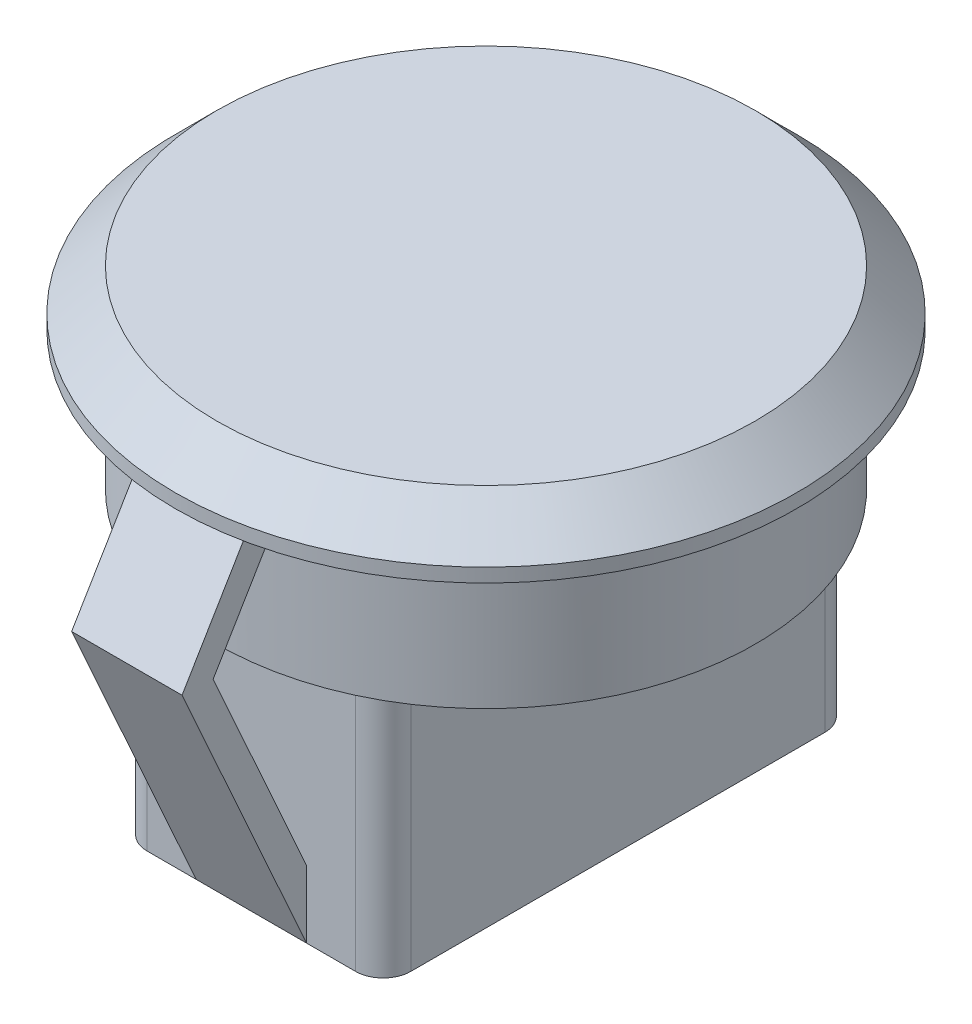
SolidWorks part; units mm, degrees
ref_plane "Спереди" through (0, 0, 0) normal (0, 0, 1) x (1, 0, 0)
ref_plane "Сверху" through (0, 0, 0) normal (0, 1, 0) x (1, 0, 0)
ref_plane "Справа" through (0, 0, 0) normal (1, 0, 0) x (0, 0, -1)
sketch "Эскиз1" plane through (0, 0, 0) normal (0, 1, 0) x (1, 0, 0)
  line L0 (-9.75, 0) -> (-12.3113, 0) construction
  line L2 (-10.75, 1) -> (-9.6986, 1)
  line L3 (-10.75, 1) -> (-10.75, -1)
  line L4 (-10.75, -1) -> (-9.6986, -1)
  arc A0 (-9.6986, -1) -> (-9.6986, 1) centre (0, 0) ccw
  point P1 (-10.75, 0)
  point P5 (0, 0)
  point P7 (-12.3113, -0.1236)
  dimension "D1" = 19.5
  dimension "D2" = 1
  dimension "D3" = 2
extrude "Бобышка-Вытянуть1" add sketch "Эскиз1" along normal blind 5
sketch "Эскиз2" plane through (0, 5, 0) normal (0, 1, 0) x (1, 0, 0)
  circle A0 centre (0, 0) radius 11.25
  dimension "D1" = 22.5
extrude "Бобышка-Вытянуть2" add sketch "Эскиз2" along normal blind 2
chamfer "Фаска1" distance 1.5 angle 45 1 edges at (0, 7, 11.25)
sketch "Эскиз3" plane through (0, 0, 0) normal (0, -1, 0) x (1, 0, 0)
  line L1 (-4.7762, 8.5) -> (4.7762, 8.5)
  line L2 (-4.7762, 8.5) -> (-4.7762, -8.5)
  line L3 (-4.7762, -8.5) -> (4.7762, -8.5)
  line L4 (4.7762, 8.5) -> (4.7762, -8.5)
  arc A0 (-9.6986, -1) -> (-9.6986, 1) centre (0, 0) ccw construction
  point P7 (0, 0)
  dimension "D1" = 17
extrude "Бобышка-Вытянуть3" add sketch "Эскиз3" along normal blind 9
fillet "Скругление1" radius 1 4 edges at (4.7762, -4.5, -8.5) (-4.7762, -4.5, -8.5) (4.7762, -4.5, 8.5) (-4.7762, -4.5, 8.5)
sketch "Эскиз4" plane through (0, 0, 0) normal (1, 0, 0) x (0, 0, -1)
  line L0 (-8.5, -9) -> (-13.0104, 1.0328)
  line L1 (-13.0104, 1.0328) -> (-10.7094, 4.9)
  line L2 (-10.7094, 4.9) -> (-9.85, 4.3887)
  line L3 (-9.85, 4.3887) -> (-11.885, 0.9684)
  line L4 (-11.885, 0.9684) -> (-7.5879, -8.59)
  line L5 (-7.5879, -8.59) -> (-8.5, -9)
  line L10 (-11.25, 5) -> (11.25, 5) construction
  line L13 (0, -1000) -> (0, 49000) construction
  line L14 (11.885, 0.9684) -> (7.5879, -8.59)
  line L15 (9.85, 4.3887) -> (11.885, 0.9684)
  line L16 (10.7094, 4.9) -> (9.85, 4.3887)
  line L17 (13.0104, 1.0328) -> (10.7094, 4.9)
  line L18 (8.5, -9) -> (13.0104, 1.0328)
  line L19 (7.5879, -8.59) -> (8.5, -9)
  line L28 (-9.75, 5) -> (9.75, 5) construction
  line L29 (-9.75, 5) -> (9.75, 5) construction
  point P15 (-8.5, 4.2745)
  point P16 (-10.7216, 4.9)
  dimension "D1" = 1
  dimension "D2" = 11
  dimension "D3" = 4.5
  dimension "D4" = 0.1
  dimension "D5" = 0.1
extrude "Бобышка-Вытянуть4" add sketch "Эскиз4" along normal mid plane 4
